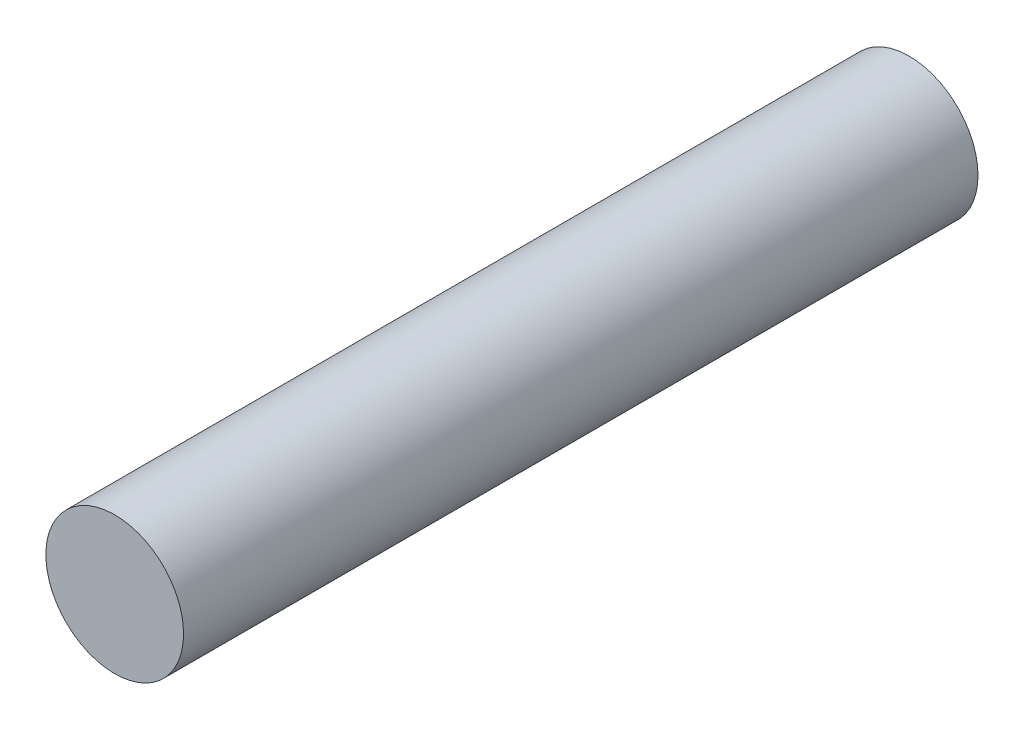
SolidWorks part; units mm, degrees
material "PA Type 6"
ref_plane "Front Plane" through (0, 0, 0) normal (0, 0, 1) x (1, 0, 0)
ref_plane "Top Plane" through (0, 0, 0) normal (0, 1, 0) x (1, 0, 0)
ref_plane "Right Plane" through (0, 0, 0) normal (1, 0, 0) x (0, 0, -1)
sketch "Sketch1" plane through (0, 0, 0) normal (0, 0, 1) x (1, 0, 0)
  circle A0 centre (0, 0) radius 6.5
  dimension "D1" = 13
extrude "Boss-Extrude1" add sketch "Sketch1" along normal mid plane 75
